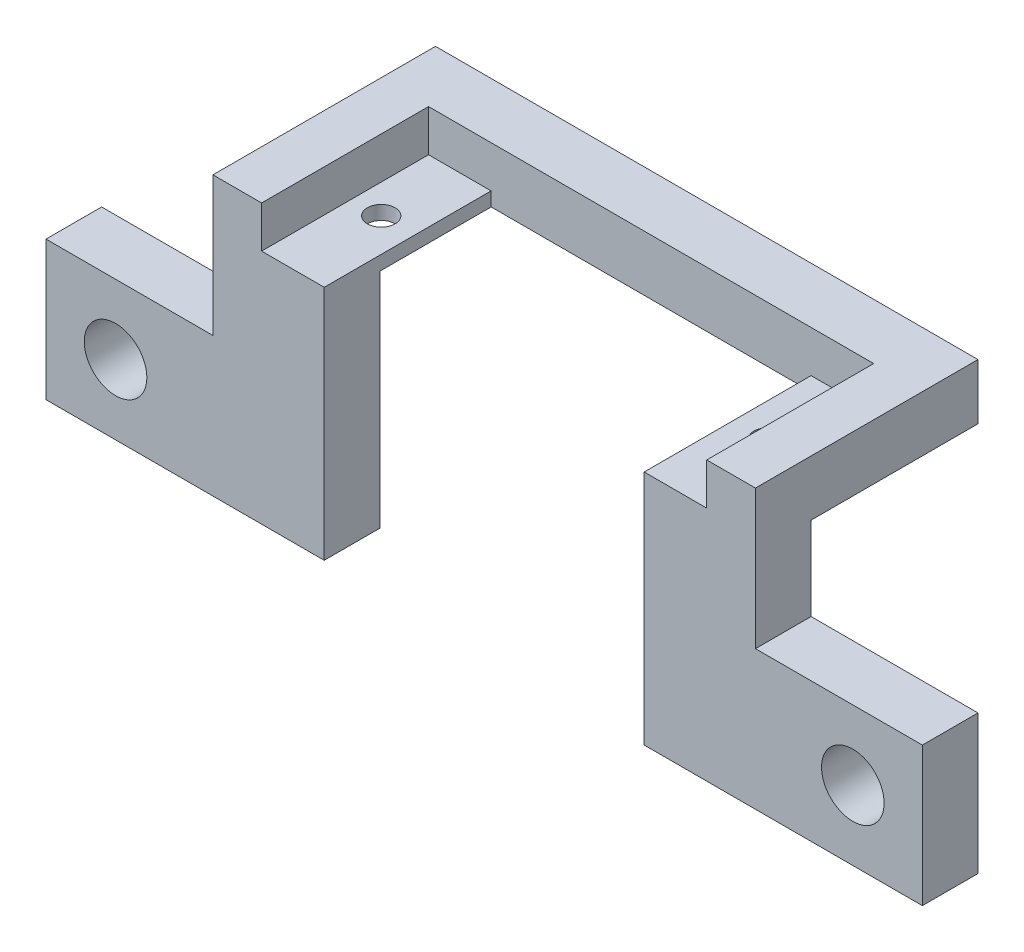
SolidWorks part; units mm, degrees
ref_plane "Plano frontal" through (0, 0, 0) normal (0, 0, 1) x (1, 0, 0)
ref_plane "Plano superior" through (0, 0, 0) normal (0, 1, 0) x (1, 0, 0)
ref_plane "Plano direito" through (0, 0, 0) normal (1, 0, 0) x (0, 0, -1)
sketch "Esboço1" plane through (0, 0, 0) normal (0, 1, 0) x (1, 0, 0)
  line L0 (-19.5, 4) -> (-19.5, -12)
  line L1 (-19.5, -12) -> (-11.5, -12)
  line L2 (-11.5, -12) -> (-11.5, 0)
  line L3 (-11.5, 0) -> (11.5, 0)
  line L4 (-19.5, 4) -> (19.5, 4)
  line L5 (0, 24.5095) -> (0, 32.033) construction
  line L6 (19.5, -12) -> (11.5, -12)
  line L7 (19.5, 4) -> (19.5, -12)
  line L8 (11.5, -12) -> (11.5, 0)
  point P6 (0, 4)
  point P14 (0, 0)
  dimension "D1" = 8
  dimension "D2" = 11.5
  dimension "D3" = 4
  dimension "D4" = 12
extrude "Ressalto-extrusão1" add sketch "Esboço1" along normal blind 4
hole_wizard "Furo de diâmetro Ø2.0 (2)1" positions "3DSketch2" profile "Esboço3" hole size "Ø2.0" standard "ISO" end condition through all
sketch3d "3DSketch2"
  line L1 (-11.5, 4, 12) -> (-11.5, 4, 0) construction
  line L2 (11.5, 4, 0) -> (11.5, 4, 12) construction
  line L3 (-19.5, 4, 12) -> (-11.5, 4, 12) construction
  line L4 (11.5, 4, 12) -> (19.5, 4, 12) construction
  point P0 (-13.9, 4, 5.5)
  point P2 (13.9, 4, 5.5)
  dimension "D1" = 6.5
  dimension "D2" = 6.5
  dimension "D3" = 2.4
  dimension "D4" = 2.4
sketch "Esboço3" plane through (-13.9, 4, 5.5) normal (1, 0, 0) x (0, 0, 1)
  line L0 (0, 0) -> (0, 4)
  line L1 (0, 4) -> (1, 4)
  line L2 (1, 4) -> (1, 0)
  line L5 (1, 0) -> (0, 0)
  line L11 (0, -6.35) -> (0, 107.95) construction
  dimension "Thru Hole Dia." = 2
  dimension "Thru Hole Depth" = 4
sketch "Esboço4" plane through (0, 0, 12) normal (0, 0, 1) x (1, 0, 0)
  line L0 (31.5, -16) -> (31.5, -6)
  line L1 (-19.5, 4) -> (-11.5, 4)
  line L2 (-19.5, 4) -> (-19.5, -6)
  line L3 (-31.5, -16) -> (-11.5, -16)
  line L4 (-11.5, 4) -> (-11.5, -16)
  line L5 (0, 0) -> (0, 9.9047) construction
  line L7 (-31.5, -16) -> (-31.5, -6)
  line L8 (-31.5, -6) -> (-19.5, -6)
  line L10 (31.5, -16) -> (11.5, -16)
  line L11 (11.5, 4) -> (11.5, -16)
  line L12 (19.5, 4) -> (11.5, 4)
  line L13 (19.5, 4) -> (19.5, -6)
  line L14 (31.5, -6) -> (19.5, -6)
  dimension "D1" = 8
  dimension "D2" = 20
  dimension "D3" = 20
  dimension "D4" = 10
extrude "Ressalto-extrusão2" add sketch "Esboço4" against normal blind 4
hole_wizard "Furo com folga de M41" positions "3DSketch3" profile "Esboço5" hole size "M4" standard "ISO" end condition through all
sketch3d "3DSketch3"
  line L0 (-31.5, -6, 12) -> (-31.5, -16, 12) construction
  line L1 (-19.5, -6, 12) -> (-31.5, -6, 12) construction
  line L2 (31.5, -16, 12) -> (31.5, -6, 12) construction
  line L3 (31.5, -6, 12) -> (19.5, -6, 12) construction
  point P0 (-26.5, -11, 12)
  point P2 (26.5, -11, 12)
  dimension "D1" = 5
  dimension "D2" = 5
  dimension "D3" = 5
  dimension "D4" = 5
sketch "Esboço5" plane through (-26.5, -11, 12) normal (1, 0, 0) x (0, -1, 0)
  line L0 (0, 0) -> (0, 16)
  line L1 (0, 16) -> (2.25, 16)
  line L2 (2.25, 16) -> (2.25, 0)
  line L5 (2.25, 0) -> (0, 0)
  line L11 (0, -6.35) -> (0, 107.95) construction
  dimension "Thru Hole Dia." = 4.5
  dimension "Thru Hole Depth" = 16
sketch "Esboço6" plane through (0, 4, 0) normal (0, 1, 0) x (1, 0, 0)
  line L1 (-16, 0) -> (16, 0)
  line L2 (-16, 0) -> (-16, -12)
  line L3 (-16, -12) -> (16, -12)
  line L4 (16, 0) -> (16, -12)
  line L5 (-13.9, -5.5) -> (-23.1081, -5.5) construction
  dimension "D1" = 12
  dimension "D2" = 32
extrude "Corte-extrusão1" cut sketch "Esboço6" against normal blind 3
